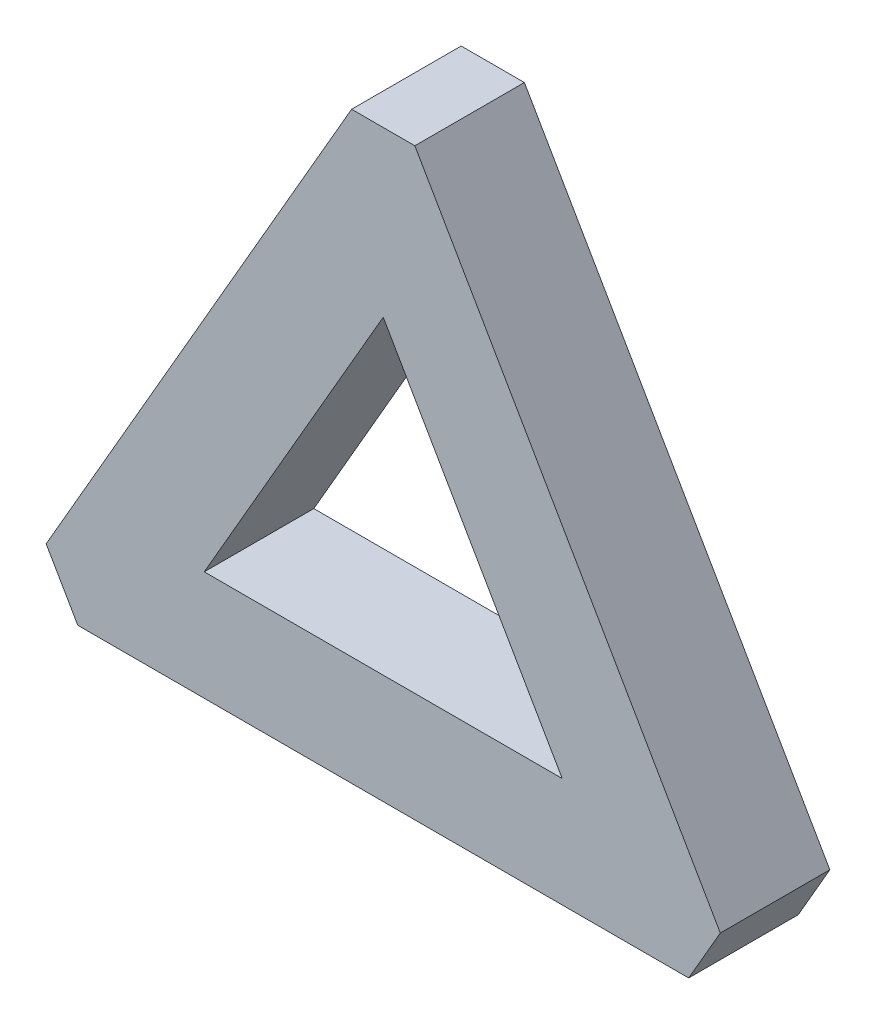
SolidWorks part; units mm, degrees
ref_plane "前视基准面" through (0, 0, 0) normal (0, 0, 1) x (1, 0, 0)
ref_plane "上视基准面" through (0, 0, 0) normal (0, 1, 0) x (1, 0, 0)
ref_plane "右视基准面" through (0, 0, 0) normal (1, 0, 0) x (0, 0, -1)
sketch "草图7" plane through (0, 0, 0) normal (0, 0, 1) x (1, 0, 0)
  line L0 (-16.9514, 8.3743) -> (0, 37.735)
  line L4 (0, 37.735) -> (18.0974, 6.3894)
  line L5 (18.0974, 6.3894) -> (32.6795, -18.8675)
  line L6 (32.6795, -18.8675) -> (0.822, -18.8675)
  line L7 (-16.9514, 8.3743) -> (-32.6795, -18.8675)
  line L8 (-32.6795, -18.8675) -> (0.822, -18.8675)
  line L9 (-33.9109, 18.9996) -> (-61.547, -28.8675)
  line L10 (-55.7735, -38.8675) -> (1.4625, -38.8675)
  line L11 (-33.9109, 18.9996) -> (-5.7735, 67.735)
  line L12 (5.7735, 67.735) -> (37.6337, 12.5516)
  line L13 (37.6337, 12.5516) -> (61.547, -28.8675)
  line L14 (55.7735, -38.8675) -> (1.4625, -38.8675)
  line L21 (-55.7735, -38.8675) -> (-61.547, -28.8675)
  line L22 (61.547, -28.8675) -> (55.7735, -38.8675)
  line L23 (-5.7735, 67.735) -> (5.7735, 67.735)
  point P0 (-16.9514, 8.3743)
  point P1 (18.0974, 6.3894)
  point P5 (0.822, -18.8675)
  point P8 (-33.9109, 18.9996)
  point P13 (37.6337, 12.5516)
  point P14 (1.4625, -38.8675)
extrude "凸台-拉伸4" add sketch "草图7" along normal blind 20
